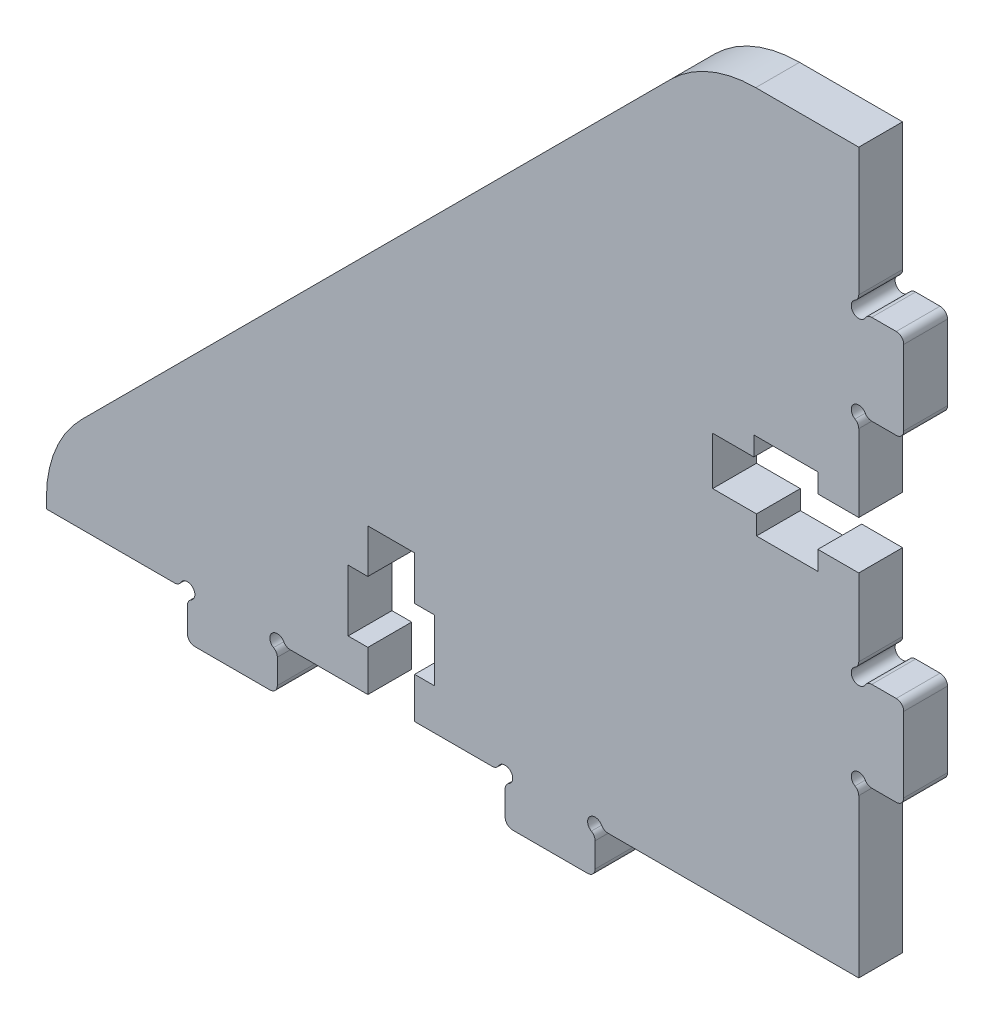
SolidWorks part; units mm, degrees
ref_plane "Front Plane" through (0, 0, 0) normal (0, 0, 1) x (1, 0, 0)
ref_plane "Top Plane" through (0, 0, 0) normal (0, 1, 0) x (1, 0, 0)
ref_plane "Right Plane" through (0, 0, 0) normal (1, 0, 0) x (0, 0, -1)
sketch "Sketch1" plane through (0, 0, 0) normal (0, 0, 1) x (1, 0, 0)
  line L0 (154.2021, 220.5549) -> (154.2021, 222.2315)
  line L1 (148.5586, 220.0418) -> (153.689, 220.0418)
  line L2 (148.0456, 222.2315) -> (148.0456, 220.5549)
  line L3 (141.8473, 223.1202) -> (147.157, 223.1202)
  line L4 (141.8473, 225.9202) -> (141.8473, 223.1202)
  line L5 (143.1973, 225.9202) -> (141.8473, 225.9202)
  line L6 (143.1973, 230.1202) -> (143.1973, 225.9202)
  line L7 (141.8473, 230.1202) -> (143.1973, 230.1202)
  line L8 (141.8473, 233.1202) -> (141.8473, 230.1202)
  line L9 (138.6473, 233.1202) -> (141.8473, 233.1202)
  line L10 (138.6473, 230.1202) -> (138.6473, 233.1202)
  line L11 (137.2973, 230.1202) -> (138.6473, 230.1202)
  line L12 (137.2973, 225.9202) -> (137.2973, 230.1202)
  line L13 (138.6473, 225.9202) -> (137.2973, 225.9202)
  line L14 (138.6473, 223.1202) -> (138.6473, 225.9202)
  line L15 (133.3377, 223.1202) -> (138.6473, 223.1202)
  line L16 (132.449, 220.5549) -> (132.449, 222.2315)
  line L17 (162.2473, 250.4141) -> (165.0647, 250.4141)
  line L18 (162.2473, 247.1306) -> (162.2473, 250.4141)
  line L19 (165.2473, 247.1306) -> (162.2473, 247.1306)
  line L20 (165.2473, 245.8223) -> (165.2473, 247.1306)
  line L21 (169.4473, 245.8223) -> (165.2473, 245.8223)
  line L22 (169.4473, 247.1306) -> (169.4473, 245.8223)
  line L23 (172.2473, 247.1306) -> (169.4473, 247.1306)
  line L24 (172.2473, 241.8627) -> (172.2473, 247.1306)
  line L25 (174.8126, 240.9741) -> (173.1359, 240.9741)
  line L26 (175.3256, 235.3306) -> (175.3256, 240.461)
  line L27 (173.1359, 234.8175) -> (174.8126, 234.8175)
  line L28 (172.2473, 223.1202) -> (172.2473, 233.9289)
  line L29 (155.0907, 223.1202) -> (172.2473, 223.1202)
  line L30 (126.8056, 220.0418) -> (131.936, 220.0418)
  line L31 (126.2925, 222.2315) -> (126.2925, 220.5549)
  line L32 (116.6473, 223.1202) -> (125.4039, 223.1202)
  line L33 (116.6473, 223.8243) -> (116.6473, 223.1202)
  line L34 (159.3909, 269.9681) -> (119.0516, 229.6288)
  line L35 (172.2473, 272.3723) -> (165.1953, 272.3723)
  line L36 (172.2473, 263.6157) -> (172.2473, 272.3723)
  line L37 (174.8126, 262.7271) -> (173.1359, 262.7271)
  line L38 (175.3256, 257.0836) -> (175.3256, 262.2141)
  line L39 (173.1359, 256.5706) -> (174.8126, 256.5706)
  line L40 (172.2473, 250.4141) -> (172.2473, 255.682)
  line L41 (169.4473, 250.4141) -> (172.2473, 250.4141)
  line L42 (169.4473, 251.7223) -> (169.4473, 250.4141)
  line L43 (165.0647, 251.7223) -> (169.4473, 251.7223)
  line L44 (165.0647, 250.4141) -> (165.0647, 251.7223)
  arc A0 (154.2021, 222.2315) -> (153.9456, 222.6758) centre (153.689, 222.2315) ccw
  arc A1 (153.689, 220.0418) -> (154.2021, 220.5549) centre (153.689, 220.5549) ccw
  arc A2 (148.0456, 220.5549) -> (148.5586, 220.0418) centre (148.5586, 220.5549) ccw
  arc A3 (148.3021, 222.6758) -> (148.0456, 222.2315) centre (148.5586, 222.2315) ccw
  arc A4 (148.3021, 222.6758) -> (147.6013, 223.3767) centre (148.0456, 223.1202) ccw
  arc A5 (147.157, 223.1202) -> (147.6013, 223.3767) centre (147.157, 223.6332) ccw
  arc A6 (132.8934, 223.3767) -> (133.3377, 223.1202) centre (133.3377, 223.6332) ccw
  arc A7 (132.8934, 223.3767) -> (132.1925, 222.6758) centre (132.449, 223.1202) ccw
  arc A8 (131.936, 220.0418) -> (132.449, 220.5549) centre (131.936, 220.5549) ccw
  arc A9 (171.9908, 241.4184) -> (172.2473, 241.8627) centre (171.7343, 241.8627) ccw
  arc A10 (171.9908, 241.4184) -> (172.6916, 240.7175) centre (172.2473, 240.9741) ccw
  arc A11 (173.1359, 240.9741) -> (172.6916, 240.7175) centre (173.1359, 240.461) ccw
  arc A12 (175.3256, 240.461) -> (174.8126, 240.9741) centre (174.8126, 240.461) ccw
  arc A13 (174.8126, 234.8175) -> (175.3256, 235.3306) centre (174.8126, 235.3306) ccw
  arc A14 (172.6916, 235.0741) -> (173.1359, 234.8175) centre (173.1359, 235.3306) ccw
  arc A15 (172.6916, 235.0741) -> (171.9908, 234.3732) centre (172.2473, 234.8175) ccw
  arc A16 (172.2473, 233.9289) -> (171.9908, 234.3732) centre (171.7343, 233.9289) ccw
  arc A17 (154.6464, 223.3767) -> (155.0907, 223.1202) centre (155.0907, 223.6332) ccw
  arc A18 (154.6464, 223.3767) -> (153.9456, 222.6758) centre (154.2021, 223.1202) ccw
  arc A19 (132.449, 222.2315) -> (132.1925, 222.6758) centre (131.936, 222.2315) ccw
  arc A20 (126.2925, 220.5549) -> (126.8056, 220.0418) centre (126.8056, 220.5549) ccw
  arc A21 (126.549, 222.6758) -> (126.2925, 222.2315) centre (126.8056, 222.2315) ccw
  arc A22 (126.549, 222.6758) -> (125.8482, 223.3767) centre (126.2925, 223.1202) ccw
  arc A23 (125.4039, 223.1202) -> (125.8482, 223.3767) centre (125.4039, 223.6332) ccw
  arc A24 (119.0516, 229.6288) -> (116.6473, 223.8243) centre (124.856, 223.8243) ccw
  arc A25 (165.1953, 272.3723) -> (159.3909, 269.9681) centre (165.1953, 264.1636) ccw
  arc A26 (171.9908, 263.1714) -> (172.2473, 263.6157) centre (171.7343, 263.6157) ccw
  arc A27 (171.9908, 263.1714) -> (172.6916, 262.4706) centre (172.2473, 262.7271) ccw
  arc A28 (173.1359, 262.7271) -> (172.6916, 262.4706) centre (173.1359, 262.2141) ccw
  arc A29 (175.3256, 262.2141) -> (174.8126, 262.7271) centre (174.8126, 262.2141) ccw
  arc A30 (174.8126, 256.5706) -> (175.3256, 257.0836) centre (174.8126, 257.0836) ccw
  arc A31 (172.6916, 256.8271) -> (173.1359, 256.5706) centre (173.1359, 257.0836) ccw
  arc A32 (172.6916, 256.8271) -> (171.9908, 256.1263) centre (172.2473, 256.5706) ccw
  arc A33 (172.2473, 255.682) -> (171.9908, 256.1263) centre (171.7343, 255.682) ccw
extrude "Boss-Extrude1" add sketch "Sketch1" along normal blind 3
